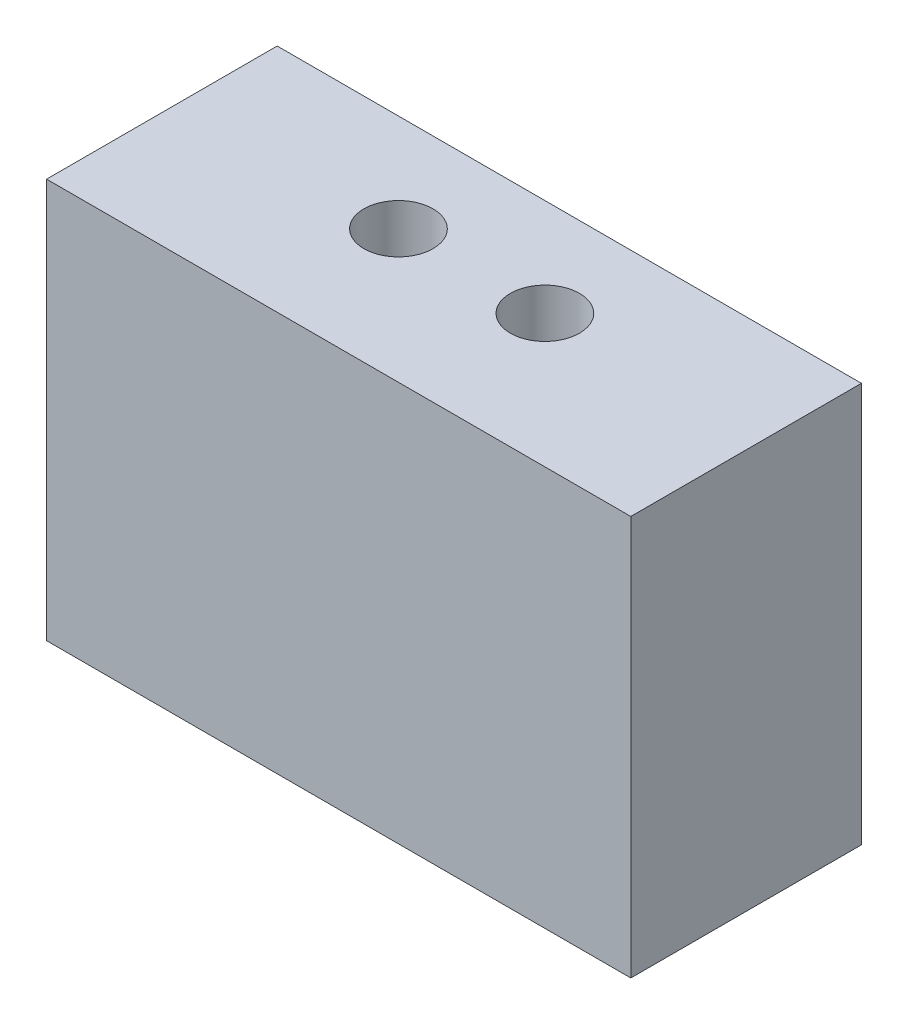
SolidWorks part; units mm, degrees
ref_plane "Front" through (0, 0, 0) normal (0, 0, 1) x (1, 0, 0)
ref_plane "Top" through (0, 0, 0) normal (0, 1, 0) x (1, 0, 0)
ref_plane "Right" through (0, 0, 0) normal (1, 0, 0) x (0, 0, -1)
sketch "Sketch1" plane through (0, 0, 0) normal (0, 0, 1) x (1, 0, 0)
  line L1 (-19, 52) -> (19, 52)
  line L2 (-19, 52) -> (-19, 0)
  line L3 (-19, 0) -> (19, 0)
  line L4 (19, 52) -> (19, 0)
  dimension "D1" = 52
  dimension "D2" = 38
extrude "Extrude1" add sketch "Sketch1" along normal blind 15
sketch "Sketch4" plane through (0, 0, 15) normal (0, 0, 1) x (1, 0, 0)
  line L1 (-19, 52) -> (19, 52)
  line L2 (-19, 52) -> (-19, 26)
  line L3 (-19, 26) -> (19, 26)
  line L4 (19, 52) -> (19, 26)
  line L5 (19, 0) -> (19, 52) construction
  dimension "D1" = 26
extrude "Cut-Extrude3" cut sketch "Sketch4" against normal through all
hole_wizard "#8 Clearance Hole2" positions "Sketch13" profile "Sketch12" hole size "#8" standard "Ansi Inch" end condition through all
sketch "Sketch13" plane through (0, 26, 0) normal (0, 1, 0) x (-1, 0, 0)
  line L0 (0, 0) -> (0, 14.3948) construction
  line L1 (19, 0) -> (-19, 0) construction
  point P0 (-4.7625, 6.35)
  point P1 (4.7625, 6.35)
  dimension "D1" = 9.525
  dimension "D2" = 6.35
sketch "Sketch12" plane through (4.7625, 26, 6.35) normal (1, 0, 0) x (0, 0, 1)
  line L0 (0, 0) -> (0, 26)
  line L1 (0, 26) -> (2.2479, 26)
  line L2 (2.2479, 26) -> (2.2479, 0)
  line L5 (2.2479, 0) -> (0, 0)
  line L11 (0, -6.35) -> (0, 107.95) construction
  dimension "Thru Hole Dia." = 4.4958
  dimension "Thru Hole Depth" = 26
